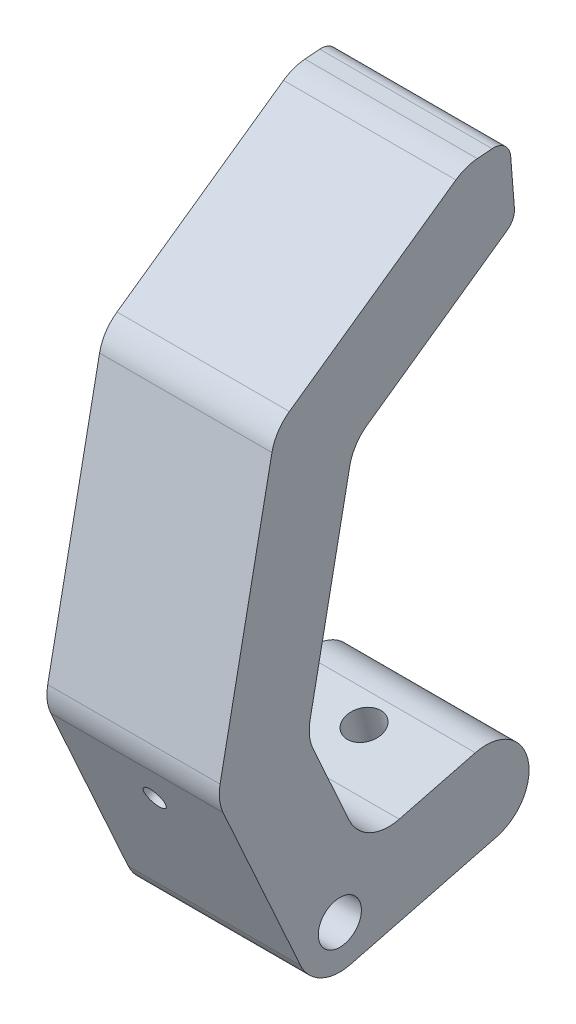
SolidWorks part; units mm, degrees
ref_plane "Front Plane" through (0, 0, 0) normal (0, 0, 1) x (1, 0, 0)
ref_plane "Top Plane" through (0, 0, 0) normal (0, 1, 0) x (1, 0, 0)
ref_plane "Right Plane" through (0, 0, 0) normal (1, 0, 0) x (0, 0, -1)
sketch "Sketch1" plane through (0, 0, 0) normal (1, 0, 0) x (0, 0, -1)
  line L0 (0, 0) -> (-11.4166, 25.2225) construction
  line L1 (-11.4166, 25.2225) -> (-3.7762, 63.7146) construction
  line L2 (-3.7762, 63.7146) -> (22.1767, 82.0041) construction
  line L3 (0, 0) -> (21.5313, 5.5095) construction
  line L4 (-9.5102, 67.4421) -> (18.5188, 87.1947)
  line L5 (-18.0418, 24.4603) -> (-9.5102, 67.4421)
  line L6 (-3.5878, -7.4727) -> (-18.0418, 24.4603)
  line L7 (-3.5878, -7.4727) -> (23.1054, -0.6423)
  line L8 (1.9578, 59.9871) -> (25.8346, 76.8136)
  line L9 (-4.7914, 25.9848) -> (1.9578, 59.9871)
  line L10 (3.5878, 7.4727) -> (-4.7914, 25.9848)
  line L11 (3.5878, 7.4727) -> (19.9571, 11.6613)
  line L12 (25.8346, 76.8136) -> (18.5188, 87.1947) construction
  line L13 (-11.4166, 25.2225) -> (-18.0418, 24.4603) construction
  line L14 (18.5188, 87.1947) -> (24.9717, 87.7059)
  line L15 (-3.7762, 63.7146) -> (22.1767, 82.0041) construction
  line L21 (24.9717, 87.7059) -> (25.8346, 76.8136)
  arc A0 (19.9571, 11.6613) -> (23.1054, -0.6423) centre (21.5313, 5.5095) cw
  circle A1 centre (0, 0) radius 3.175
  dimension "D10" = 6.35
  dimension "D1" = 27.686
  dimension "D2" = 39.243
  dimension "D3" = 31.75
  dimension "D4" = 144.42
  dimension "D5" = 136.4
  dimension "D6" = 22.225
  dimension "D7" = 100
  dimension "D12" = 6.4731
  dimension "D8" = 6.35
  dimension "D9" = 6.35
extrude "Boss-Extrude1" add sketch "Sketch1" along normal blind 25.4
fillet "Fillet1" radius 6.35 7 edges at (12.7, 7.4727, -3.5878) (12.7, 25.9848, 4.7914) (12.7, 59.9871, -1.9578) (12.7, 67.4421, 9.5102) (12.7, 24.4603, 18.0418) (12.7, -7.4727, 3.5878) (12.7, 87.1947, -18.5188)
sketch "Sketch2" plane through (0, -6.1518, -1.5742) normal (0, -0.9688, -0.2479) x (1, 0, 0)
  line L0 (0, -18.415) -> (25.4, -18.415) construction
  line L1 (0, 0) -> (0, -22.225) construction
  line L2 (25.4, 0) -> (25.4, -22.225) construction
  line L3 (25.4, -18.415) -> (12.7, -18.415) construction
  line L4 (12.7, -18.415) -> (24.1766, -18.415) construction
  line L5 (25.4, -22.225) -> (0, -22.225) construction
  circle A0 centre (12.7, -18.415) radius 2.54
  dimension "D1" = 5.08
  dimension "D2" = 3.81
extrude "Cut-Extrude1" cut sketch "Sketch2" against normal up to next
sketch "Sketch3" plane through (0, -2.6185, 5.785) normal (0, -0.4124, 0.911) x (1, 0, 0)
  line L0 (12.7, 27.686) -> (12.7, 21.336) construction
  line L1 (25.4, 27.686) -> (0, 27.686) construction
  circle A0 centre (12.7, 21.336) radius 1.5875
  dimension "D2" = 3.175
  dimension "D1" = 6.35
extrude "Cut-Extrude2" cut sketch "Sketch3" against normal up to next
fillet "Fillet2" radius 2.54 2 edges at (12.7, 76.8136, -25.8346) (12.7, 87.7059, -24.9717)
